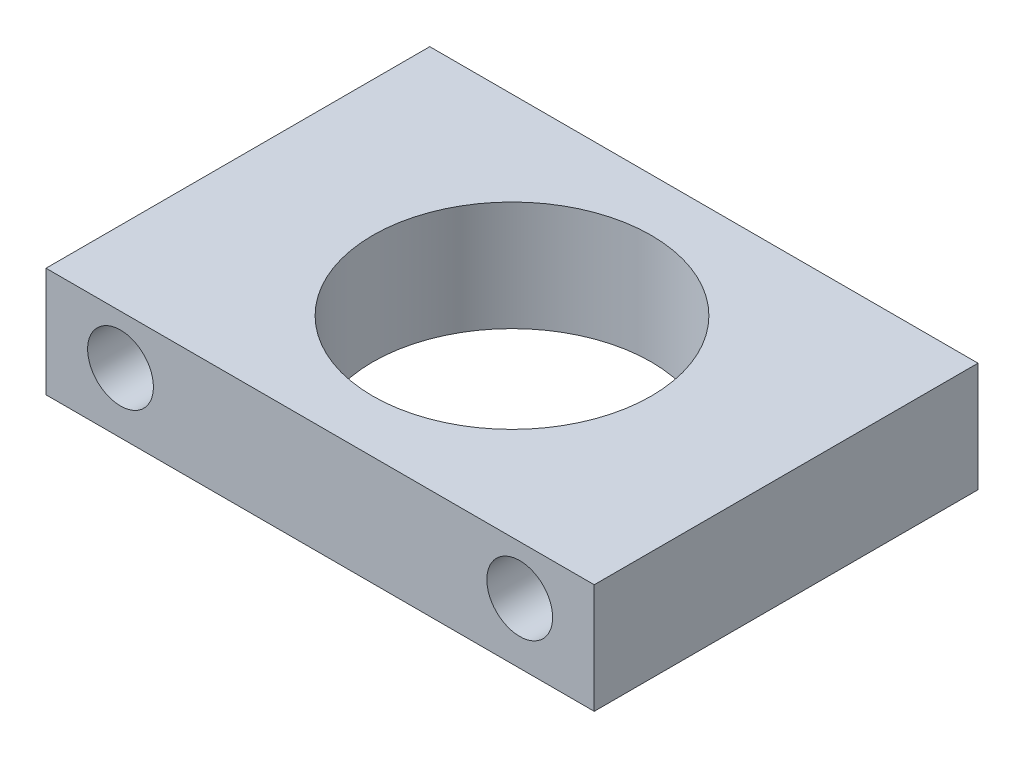
SolidWorks part; units mm, degrees
ref_plane "Front" through (0, 0, 0) normal (0, 0, 1) x (1, 0, 0)
ref_plane "Top" through (0, 0, 0) normal (0, 1, 0) x (1, 0, 0)
ref_plane "Right" through (0, 0, 0) normal (1, 0, 0) x (0, 0, -1)
sketch "Sketch1" plane through (0, 0, 0) normal (0, 1, 0) x (1, 0, 0)
  line L0 (0, -17.5) -> (0, 17.5) construction
  line L1 (-25, 17.5) -> (25, 17.5)
  line L2 (-25, 17.5) -> (-25, -17.5)
  line L3 (-25, -17.5) -> (25, -17.5)
  line L4 (25, 17.5) -> (25, -17.5)
  line L5 (0, 0) -> (-25, 0) construction
  circle A0 centre (0, 0) radius 12.7
  point P9 (0, 0)
  dimension "D1" = 35
  dimension "D3" = 25.4
  dimension "D2" = 50
  dimension "D4" = 17.5
  dimension "D5" = 25
extrude "Boss-Extrude1" add sketch "Sketch1" along normal blind 10
sketch "Sketch2" plane through (0, 0, 17.5) normal (0, 0, 1) x (1, 0, 0)
  line L0 (18.2034, 5.5159) -> (-18.2034, 5.5159) construction
  circle A0 centre (-18.2034, 5.5159) radius 3
  circle A1 centre (18.2034, 5.5159) radius 3
  point P3 (0, 5.5159)
extrude "Cut-Extrude1" cut sketch "Sketch2" against normal blind 62
